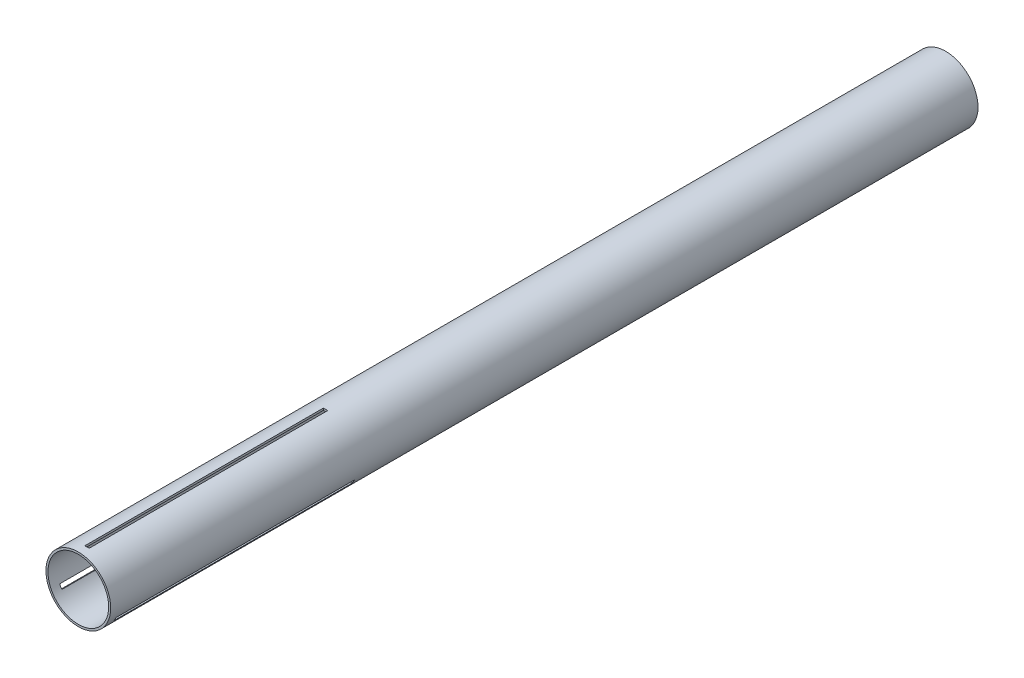
SolidWorks part; units mm, degrees
ref_plane "Front Plane" through (0, 0, 0) normal (0, 0, 1) x (1, 0, 0)
ref_plane "Top Plane" through (0, 0, 0) normal (0, 1, 0) x (1, 0, 0)
ref_plane "Right Plane" through (0, 0, 0) normal (1, 0, 0) x (0, 0, -1)
sketch "Sketch1" plane through (0, 0, 0) normal (0, 0, 1) x (1, 0, 0)
  circle A0 centre (0, 0) radius 23.6982
  circle A1 centre (0, 0) radius 22.225
extrude "Boss-Extrude1" add sketch "Sketch1" along normal blind 635
ref_plane "Plane1" through (0, 50.8, 0) normal (0, 1, 0) x (1, 0, 0)
sketch "Sketch3" plane through (0, 50.8, 0) normal (0, 1, 0) x (1, 0, 0)
  line L0 (-23.6982, -635) -> (23.6982, -635) construction
  line L2 (1.5875, -628.65) -> (1.5875, -454.025)
  line L3 (-1.5875, -628.65) -> (-1.5875, -454.025)
  line L4 (-1.5875, -454.025) -> (1.5875, -454.025)
  line L5 (-1.5875, -628.65) -> (1.5875, -628.65)
  dimension "D1" = 6.35
extrude "Cut-Extrude2" cut sketch "Sketch3" against normal up to next and the other way through all
pattern_circular "CirPattern4" count 3 over 360 about axis through (0, 0, 0) along (0, 0, 1) of "Cut-Extrude2"
